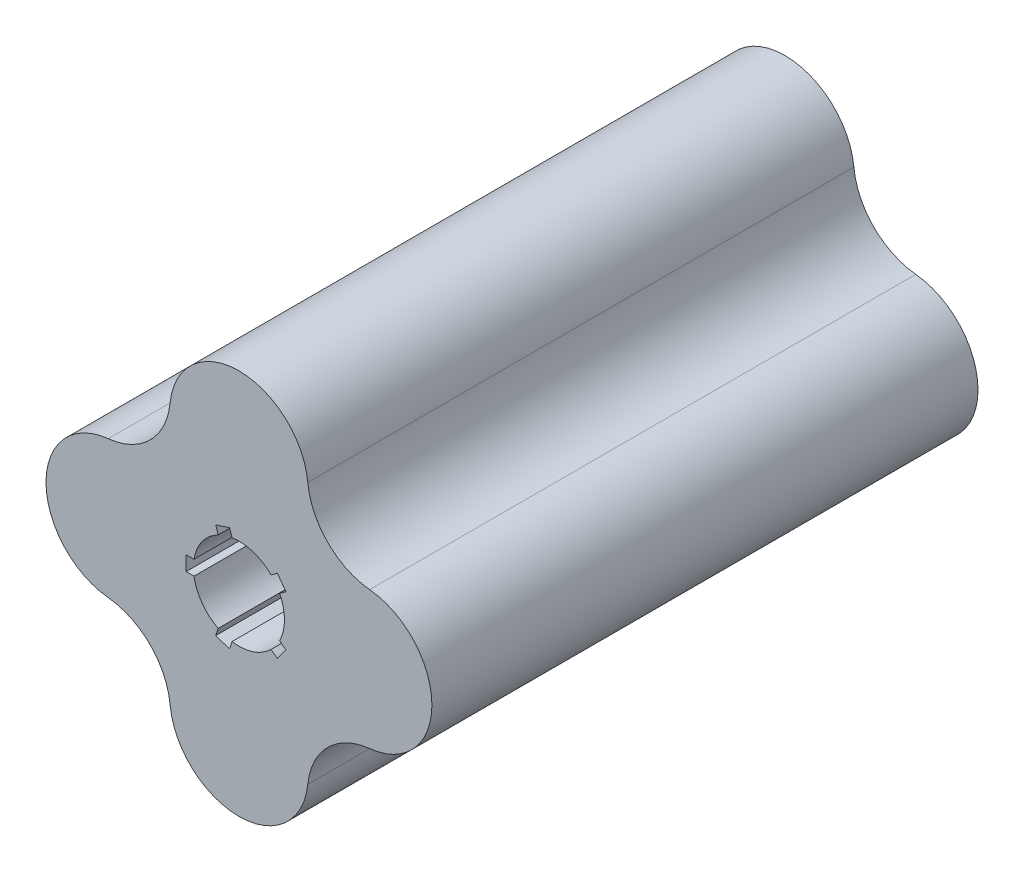
SolidWorks part; units mm, degrees
ref_plane "Front Plane" through (0, 0, 0) normal (0, 0, 1) x (1, 0, 0)
ref_plane "Top Plane" through (0, 0, 0) normal (0, 1, 0) x (1, 0, 0)
ref_plane "Right Plane" through (0, 0, 0) normal (1, 0, 0) x (0, 0, -1)
sketch "Sketch1" plane through (0, 0, 0) normal (0, 0, 1) x (1, 0, 0)
  circle A0 centre (0, 0) radius 12.5
  circle A1 centre (34, 0) radius 19
  circle A2 centre (0, -34) radius 19
  circle A3 centre (-34, 0) radius 19
  circle A4 centre (0, 34) radius 19
  arc A5 (18.9043, 35.9043) -> (35.9043, 18.9043) centre (37.8087, 37.8087) ccw
  arc A6 (35.9043, -18.9043) -> (18.9043, -35.9043) centre (37.8087, -37.8087) ccw
  arc A7 (-18.9043, -35.9043) -> (-35.9043, -18.9043) centre (-37.8087, -37.8087) ccw
  arc A8 (-35.9043, 18.9043) -> (-18.9043, 35.9043) centre (-37.8087, 37.8087) ccw
  point P14 (0, 0)
  point P27 (0, 0)
  dimension "D1" = 34
  dimension "D3" = 38
  dimension "D4" = 19
  dimension "D5" = 4
  dimension "D6" = 25
  dimension "D2" = 4
extrude "Boss-Extrude1" add sketch "Sketch1" along normal blind 150 contours A8 A3 A7 A2 A6 A1 A5 A4 A0 | A4 | A3 | A2 | A1
sketch "Sketch2" plane through (0, 0, 0) normal (0, 0, -1) x (-1, 0, 0)
  line L1 (10.5, 2) -> (14.5, 2)
  line L2 (10.5, 2) -> (10.5, -2)
  line L3 (10.5, -2) -> (14.5, -2)
  line L4 (14.5, 2) -> (14.5, -2)
  line L5 (10.5, 2) -> (14.5, -2) construction
  line L6 (10.5, -2) -> (14.5, 2) construction
  circle A0 centre (0, 0) radius 12.5 construction
  point P0 (12.5, 0)
  dimension "D1" = 4
  dimension "D2" = 4
extrude "Cut-Extrude1" cut sketch "Sketch2" against normal through all
pattern_circular "CirPattern1" count 5 over 360 about axis through (0, 0, 0) along (0, 0, 1) of "Cut-Extrude1"
